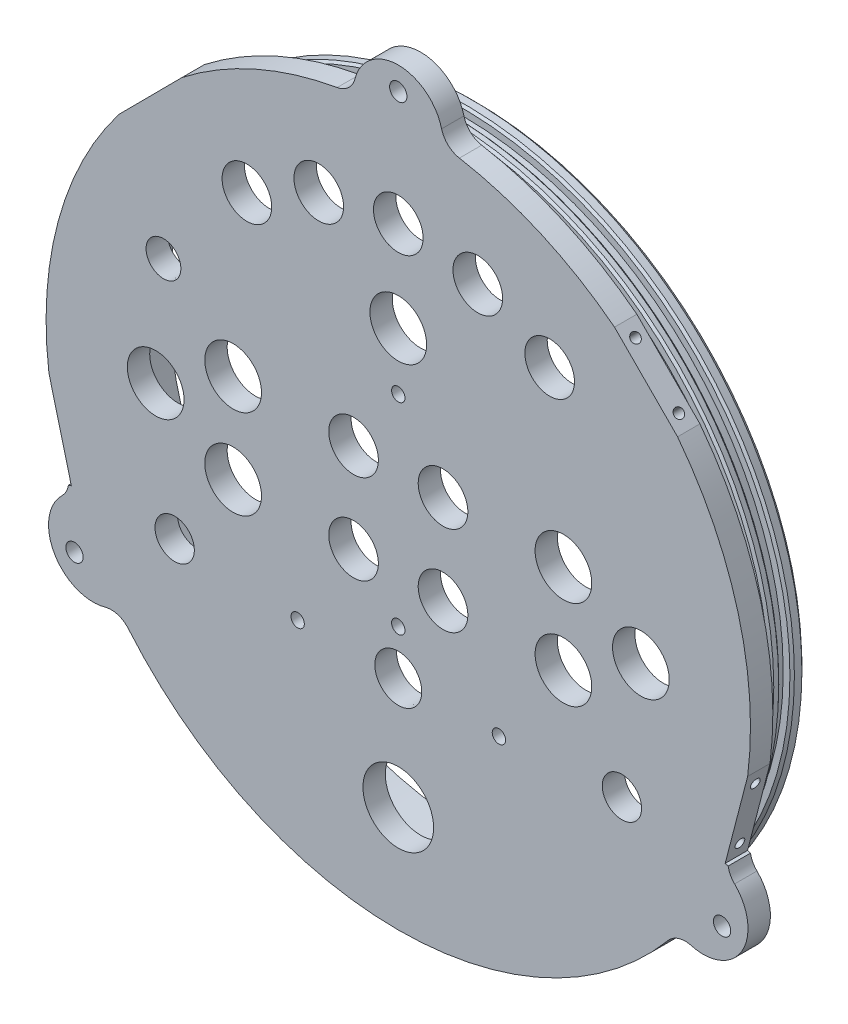
SolidWorks part; units mm, degrees
material "6061 Alloy"
ref_plane "Front Plane" through (0, 0, 0) normal (0, 0, 1) x (1, 0, 0)
ref_plane "Top Plane" through (0, 0, 0) normal (0, 1, 0) x (1, 0, 0)
ref_plane "Right Plane" through (0, 0, 0) normal (1, 0, 0) x (0, 0, -1)
sketch "Sketch1" plane through (0, 0, 0) normal (0, 0, 1) x (1, 0, 0)
  circle A0 centre (0, 0) radius 100.0125
extrude "Extrude1" add sketch "Sketch1" along normal blind 6.35
sketch "Sketch2" plane through (0, 0, 0) normal (0, 0, -1) x (-1, 0, 0)
  circle A0 centre (0, 0) radius 93.6625
extrude "Extrude2" add sketch "Sketch2" along normal blind 15.875
sketch "Sketch3" plane through (0, 0, -15.875) normal (0, 0, -1) x (-1, 0, 0)
  circle A0 centre (0, 0) radius 87.3125
extrude "Cut-Extrude1" cut sketch "Sketch3" against normal blind 15.875
sketch "Sketch4" plane through (0, 0, 0) normal (1, 0, 0) x (0, 0, -1)
  line L0 (15.875, 93.6625) -> (0, 93.6625) construction
  line L1 (2.8084, 93.6625) -> (5.9834, 93.6625)
  line L2 (2.8084, 93.6625) -> (2.8084, 91.1225)
  line L3 (2.8084, 91.1225) -> (5.9834, 91.1225)
  line L4 (5.9834, 93.6625) -> (5.9834, 91.1225)
  line L5 (0, 0) -> (42.3826, 0) construction
  line L6 (8.6645, 93.6625) -> (11.8395, 93.6625)
  line L7 (8.6645, 93.6625) -> (8.6645, 91.1225)
  line L8 (8.6645, 91.1225) -> (11.8395, 91.1225)
  line L9 (11.8395, 93.6625) -> (11.8395, 91.1225)
  dimension "D1" = 2.54
  dimension "D2" = 3.175
revolve "Cut-Revolve1" cut sketch "Sketch4" angle 360 about L5
chamfer "Chamfer1" distance 1.27 angle 45 1 edges at (-93.6625, 0, -15.875)
sketch "Sketch5" plane through (0, 0, 6.35) normal (0, 0, 1) x (1, 0, 0)
  circle A16 centre (0, 47.9573) radius 8.05
  circle A17 centre (0, 73.66) radius 7.05
  circle A18 centre (-63.5, -35.56) radius 5.588
  circle A19 centre (63.5, -35.56) radius 5.588
  dimension "D1" = 63.5
  dimension "D5" = 35.56
  dimension "D2" = 63.5
  dimension "D4" = 73.66
  dimension "D6" = 35.56
sketch "Sketch7" plane through (0, 0, 6.35) normal (0, 0, 1) x (1, 0, 0)
  line L0 (0, 0) -> (0, 100.0125) construction
  circle A0 centre (0, 0) radius 100.0125 construction
sketch "Sketch8" plane through (0, 0, 6.35) normal (0, 0, 1) x (1, 0, 0)
  line L0 (0, 0) -> (86.6134, -50.0063) construction
  line L1 (0, 0) -> (-86.6134, -50.0063) construction
  line L2 (0, 0) -> (0, 100.0125) construction
  circle A0 centre (0, 0) radius 100.0125 construction
  arc A1 (-12.6744, 99.2062) -> (12.6744, 99.2062) centre (0, 100.0125) cw
  arc A2 (92.2522, -38.6267) -> (79.5779, -60.5794) centre (86.6134, -50.0063) cw
  arc A3 (-92.2522, -38.6267) -> (-79.5779, -60.5794) centre (-86.6134, -50.0063) ccw
  arc A4 (-12.6744, 99.2062) -> (12.6744, 99.2062) centre (0, 0) cw
  arc A5 (92.2522, -38.6267) -> (79.5779, -60.5794) centre (0, 0) cw
  arc A6 (-92.2522, -38.6267) -> (-79.5779, -60.5794) centre (0, 0) ccw
  dimension "D1" = 12.7
  dimension "D2" = 12.7
  dimension "D3" = 12.7
  dimension "D4" = 120
  dimension "D5" = 120
extrude "Extrude3" add sketch "Sketch8" against normal up to surface (6.35 mm away) up to face at (100.0125, 0, 0)
sketch "Sketch10" plane through (0, 0, 6.35) normal (0, 0, 1) x (1, 0, 0)
  line L0 (0, 0) -> (0, 123.4907) construction
  line L1 (0, 0) -> (137.3268, -79.2857) construction
  line L2 (0, 0) -> (-146.5837, -84.6301) construction
extrude "Cut-Extrude2" cut sketch "Sketch5" against normal through all
hole_wizard "#10 (0.1935) Diameter Hole1" positions "3DSketch2" profile "Sketch11" hole size "#10" standard "Ansi Inch"
sketch3d "3DSketch2"
  line L0 (0, 0, 6.35) -> (0, 123.4907, 6.35) construction
  line L1 (0, 0, 6.35) -> (137.3268, -79.2857, 6.35) construction
  line L2 (0, 0, 6.35) -> (-146.5837, -84.6301, 6.35) construction
  point P0 (0, 106.1728, 6.35)
  point P4 (91.9483, -53.0864, 6.35)
  point P8 (-91.9483, -53.0864, 6.35)
  dimension "D1" = 106.3625
  dimension "D2" = 106.3625
  dimension "D3" = 106.3625
sketch "Sketch11" plane through (0, 106.1728, 6.35) normal (1, 0, 0) x (0, -1, 0)
  line L0 (0, 0) -> (0, 331.6766)
  line L1 (0, 331.6766) -> (2.4574, 330.2)
  line L2 (2.4574, 330.2) -> (2.4574, 0)
  line L5 (2.4574, 0) -> (0, 0)
  line L10 (0, 331.6766) -> (-2.4575, 330.2) construction
  line L11 (0, -6.35) -> (0, 107.95) construction
  dimension "Hole Dia." = 4.9149
  dimension "Hole Depth" = 330.2
  dimension "Drill Angle" = 118
chamfer "Chamfer2" distance 0.635 angle 45 4 edges at (93.6625, 0, -2.8084) (93.6625, 0, -5.9834) (93.6625, 0, -8.6645) (93.6625, 0, -11.8395)
sketch "Sketch15" plane through (0, 0, 6.35) normal (0, 0, 1) x (1, 0, 0)
  circle A0 centre (0, -69.85) radius 10.033
  dimension "D1" = 69.85
extrude "Cut-Extrude3" cut sketch "Sketch15" against normal through all
sketch "Sketch17" plane through (0, 0, 6.35) normal (0, 0, 1) x (1, 0, 0)
  line L0 (0, 106.1728) -> (0, 0) construction
  line L1 (-46.896, 12.7) -> (-46.896, -12.7) construction
  line L2 (-46.896, 0) -> (-107.9684, 0) construction
  line L3 (46.896, 0) -> (107.9684, 0) construction
  line L4 (46.896, 12.7) -> (46.896, -12.7) construction
  line L5 (0, 0) -> (-129.2921, 0) construction
  line L6 (68.8931, 0) -> (46.896, 12.7) construction
  line L7 (42.9911, 59.8127) -> (22.5831, 70.1128) construction
  line L8 (22.5831, 70.1128) -> (0, 73.66) construction
  line L9 (22.5831, 70.1128) -> (30.6624, 95.1962) construction
  line L10 (30.6624, 95.1962) -> (60.9252, 85.4486) construction
  line L11 (42.9911, 59.8127) -> (58.3716, 81.2112) construction
  line L12 (58.3716, 81.2112) -> (94.3714, 55.3359) construction
  line L13 (0, 0) -> (22.5831, 70.1128) construction
  line L14 (22.5831, 70.1128) -> (0, 73.66) construction
  line L15 (0, 73.66) -> (0, 0) construction
  line L16 (12.7, -12.7) -> (12.7, 0) construction
  line L17 (12.7, 12.7) -> (0, 12.7) construction
  line L19 (12.7, 0) -> (12.7, 12.7) construction
  circle A0 centre (-22.5831, 70.1128) radius 7.05
  circle A1 centre (-42.9911, 59.8127) radius 7.05
  circle A2 centre (-68.8931, 0) radius 8.05
  circle A3 centre (-46.896, -12.7) radius 8.05
  circle A4 centre (-46.896, 12.7) radius 8.05
  circle A5 centre (-12.7, 12.7) radius 7.05
  circle A6 centre (-12.7, -12.7) radius 7.05
  circle A7 centre (12.7, -12.7) radius 7.05
  circle A8 centre (12.7, 12.7) radius 7.05
  circle A9 centre (46.896, 12.7) radius 8.05
  circle A10 centre (46.896, -12.7) radius 8.05
  circle A11 centre (68.8931, 0) radius 8.05
  circle A12 centre (42.9911, 59.8127) radius 7.05
  circle A13 centre (22.5831, 70.1128) radius 7.05
  circle A15 centre (0, 0) radius 100.0125 construction
  dimension "D1" = 25.4
  dimension "D2" = 25.4
  dimension "D3" = 25.4
  dimension "D4" = 22.86
extrude "Cut-Extrude4" cut sketch "Sketch17" against normal through all
hole_wizard "#6 Clearance Hole1" positions "3DSketch7" profile "Sketch18" hole size "#6" standard "Ansi Inch"
sketch3d "3DSketch7"
  line L0 (0, 0, 0) -> (55.3338, 0, 0) construction
  line L2 (0, 0, 0) -> (0, -54.9677, 0) construction
  point P17 (28.575, -38.1, 0)
  point P19 (-28.575, -38.1, 0)
  dimension "D1" = 57.15
  dimension "D3" = 38.1
  dimension "D2" = 28.575
sketch "Sketch18" plane through (28.575, -38.1, 0) normal (1, 0, 0) x (0, 1, 0)
  line L0 (0, 0) -> (0, 13.8408)
  line L1 (0, 13.8408) -> (1.8986, 12.7)
  line L2 (1.8986, 12.7) -> (1.8986, 0)
  line L5 (1.8986, 0) -> (0, 0)
  line L10 (0, 13.8408) -> (-1.8987, 12.7) construction
  line L11 (0, -6.35) -> (0, 107.95) construction
  dimension "Hole Dia." = 3.7973
  dimension "Hole Depth" = 12.7
  dimension "Drill Angle" = 118
hole_wizard "Tap Drill for #6 Tap1" positions "3DSketch8" profile "Sketch19" hole size "#6-32" standard "Ansi Inch"
sketch3d "3DSketch8"
  line L0 (0, 0, 0) -> (-45.7945, 0, 0) construction
  line L2 (0, 0, 0) -> (0, 34.2452, 0) construction
  point P0 (34.925, 29.21, 0)
  point P2 (-34.925, 29.21, 0)
  point P4 (-25.4, 29.21, 0)
  point P6 (25.4, 29.21, 0)
  point P15 (44.45, -52.705, 0)
  point P17 (-44.45, -52.705, 0)
  dimension "D1" = 9.525
  dimension "D2" = 9.525
  dimension "D3" = 69.85
  dimension "D4" = 34.925
  dimension "D5" = 29.21
  dimension "D6" = 88.9
  dimension "D7" = 52.705
  dimension "D8" = 44.45
sketch "Sketch19" plane through (34.925, 29.21, 0) normal (1, 0, 0) x (0, 1, 0)
  line L0 (0, 0) -> (0, 4.1147)
  line L1 (0, 4.1147) -> (1.3525, 3.302)
  line L2 (1.3525, 3.302) -> (1.3525, 0)
  line L5 (1.3525, 0) -> (0, 0)
  line L10 (0, 4.1147) -> (-1.3526, 3.302) construction
  line L11 (0, -6.35) -> (0, 107.95) construction
  dimension "Hole Dia." = 2.7051
  dimension "Hole Depth" = 3.302
  dimension "Drill Angle" = 118
hole_wizard "1/4 NPT Tapped Hole1" positions "3DSketch9" profile "Sketch20" size "1/4" standard "Ansi Inch"
sketch3d "3DSketch9"
  line L0 (0, 0, 0) -> (0, -87.3125, 0) construction
  line L2 (0, 0, 0) -> (87.3125, 0, 0) construction
  circle A0 centre (0, 0, 0) radius 87.3125 construction
  point P9 (0, -38.1, 0)
  point P20 (0, 0, -87.3125)
  dimension "D2" = 38.1
sketch "Sketch20" plane through (0, -38.1, 0) normal (1, 0, 0) x (0, 1, 0)
  line L0 (0, 0) -> (0, 20.3603)
  line L1 (5.5626, 17.018) -> (0, 20.3603)
  line L2 (-5.5626, 17.018) -> (0, 20.3603) construction
  line L3 (5.5626, 17.018) -> (5.5626, 9.906)
  line L4 (5.5626, 9.906) -> (6.558, 9.906)
  line L5 (6.558, 9.906) -> (6.8546, 0)
  line L6 (-6.558, 9.906) -> (-6.8546, 0) construction
  line L7 (6.8546, 0) -> (0, 0)
  line L8 (0, -6.35) -> (0, 107.95) construction
  line L11 (-5.5626, 9.906) -> (-6.558, 9.906) construction
  dimension "Tap Drill Dia." = 11.1252
  dimension "Tap Drill Depth" = 17.018
  dimension "Thread Dia." = 13.7092
  dimension "Thread Angle" = 3.43
  dimension "Thread Depth" = 9.906
  dimension "Drill Angle" = 118
hole_wizard "1/8 NPT Tapped Hole1" positions "3DSketch6" profile "Sketch16" size "1/8" standard "Ansi Inch"
sketch3d "3DSketch6"
  line L0 (0, 0, 0) -> (87.3125, 0, 0) construction
  line L2 (0, 0, 0) -> (0, 87.3125, 0) construction
  circle A0 centre (0, 0, 0) radius 87.3125 construction
  point P3 (-66.675, 31.75, 0)
  point P10 (0, 0, -87.3125)
  dimension "D1" = 31.75
  dimension "D2" = 66.675
sketch "Sketch16" plane through (-66.675, 31.75, 0) normal (1, 0, 0) x (0, 1, 0)
  line L0 (0, 0) -> (0, 13.7095)
  line L1 (4.2164, 11.176) -> (0, 13.7095)
  line L2 (-4.2164, 11.176) -> (0, 13.7095) construction
  line L3 (4.2164, 11.176) -> (4.2164, 6.35)
  line L4 (4.2164, 6.35) -> (4.9362, 6.35)
  line L5 (4.9362, 6.35) -> (5.1263, 0)
  line L6 (-4.9362, 6.35) -> (-5.1263, 0) construction
  line L7 (5.1263, 0) -> (0, 0)
  line L8 (0, -6.35) -> (0, 107.95) construction
  line L11 (-4.2164, 6.35) -> (-4.9362, 6.35) construction
  dimension "Tap Drill Dia." = 8.4328
  dimension "Tap Drill Depth" = 11.176
  dimension "Thread Dia." = 10.2526
  dimension "Thread Angle" = 3.43
  dimension "Thread Depth" = 6.35
  dimension "Drill Angle" = 118
fillet "Fillet1" radius 6.35 6 edges at (92.2522, -38.6267, 3.175) (79.5779, -60.5794, 3.175) (-12.6744, 99.2062, 3.175) (12.6744, 99.2062, 3.175) (-79.5779, -60.5794, 3.175) (-92.2522, -38.6267, 3.175)
sketch "Sketch22" plane through (0, 0, 6.35) normal (0, 0, 1) x (1, 0, 0)
  line L0 (0, 0) -> (0, 100.0125) construction
  line L1 (-79.302, 60.94) -> (-70.3475, 69.946)
  line L2 (-70.9217, 70.5168) -> (0, 0) construction
  line L3 (0, 0) -> (-96.8054, -25.1239) construction
  line L4 (-70.3475, 69.946) -> (-61.393, 78.9519)
  line L5 (-99.2121, -12.6278) -> (-96.0218, -24.9205)
  line L6 (-96.0218, -24.9205) -> (-92.8314, -37.2133)
  line L7 (-79.302, 60.94) -> (-84.7318, 66.3388)
  line L8 (-66.8227, 84.3506) -> (-61.393, 78.9519)
  line L9 (-84.7318, 66.3388) -> (-66.8227, 84.3506)
  line L10 (-92.8314, -37.2133) -> (-99.2121, -38.8693)
  line L11 (-99.2121, -38.8693) -> (-105.5928, -14.2838)
  line L12 (-105.5928, -14.2838) -> (-99.2121, -12.6278)
  line L13 (105.5928, -14.2838) -> (99.2121, -12.6278)
  line L14 (99.2121, -38.8693) -> (105.5928, -14.2838)
  line L15 (92.8314, -37.2133) -> (99.2121, -38.8693)
  line L16 (84.7318, 66.3388) -> (66.8227, 84.3506)
  line L17 (66.8227, 84.3506) -> (61.393, 78.9519)
  line L18 (79.302, 60.94) -> (84.7318, 66.3388)
  line L19 (96.0218, -24.9205) -> (92.8314, -37.2133)
  line L20 (99.2121, -12.6278) -> (96.0218, -24.9205)
  line L21 (70.3475, 69.946) -> (61.393, 78.9519)
  line L22 (79.302, 60.94) -> (70.3475, 69.946)
  circle A0 centre (0, 0) radius 100.0125 construction
  dimension "D1" = 45.164
  dimension "D2" = 104.549
  dimension "D3" = 25.4
  dimension "D4" = 25.4
  dimension "D5" = 12.7
  dimension "D6" = 12.7
extrude "Cut-Extrude5" cut sketch "Sketch22" against normal through all
hole_wizard "Tap Drill for #6 Tap2" positions "3DSketch11" profile "Sketch23" hole size "#6-32" standard "Ansi Inch"
sketch3d "3DSketch11"
  line L0 (61.393, 78.9519, 3.175) -> (79.302, 60.94, 3.175) construction
  line L1 (61.393, 78.9519, 0) -> (61.393, 78.9519, 6.35) construction
  line L2 (79.302, 60.94, 0) -> (79.302, 60.94, 6.35) construction
  line L4 (99.2121, -12.6278, 3.175) -> (92.8314, -37.2133, 3.175) construction
  line L5 (99.2121, -12.6278, 0) -> (99.2121, -12.6278, 6.35) construction
  line L6 (92.8314, -37.2133, 0) -> (92.8314, -37.2133, 6.35) construction
  line L8 (-92.8314, -37.2133, 3.175) -> (-99.2121, -12.6278, 3.175) construction
  line L9 (-92.8314, -37.2133, 0) -> (-92.8314, -37.2133, 6.35) construction
  line L10 (-99.2121, -12.6278, 0) -> (-99.2121, -12.6278, 6.35) construction
  line L12 (-61.393, 78.9519, 3.175) -> (-79.302, 60.94, 3.175) construction
  line L13 (-61.393, 78.9519, 0) -> (-61.393, 78.9519, 6.35) construction
  line L14 (-79.302, 60.94, 0) -> (-79.302, 60.94, 6.35) construction
  line L16 (-96.0218, -24.9205, 6.35) -> (-96.0218, -24.9205, 0) construction
  line L17 (-92.8314, -37.2133, 6.35) -> (-99.2121, -12.6278, 6.35) construction
  line L18 (-92.8314, -37.2133, 0) -> (-99.2121, -12.6278, 0) construction
  line L20 (-70.3475, 69.946, 6.35) -> (-70.3475, 69.946, 0) construction
  line L21 (-79.302, 60.94, 6.35) -> (-61.393, 78.9519, 6.35) construction
  line L22 (-79.302, 60.94, 0) -> (-61.393, 78.9519, 0) construction
  line L24 (70.3475, 69.946, 6.35) -> (70.3475, 69.946, 0) construction
  line L25 (61.393, 78.9519, 6.35) -> (79.302, 60.94, 6.35) construction
  line L26 (61.393, 78.9519, 0) -> (79.302, 60.94, 0) construction
  line L28 (96.0218, -24.9205, 6.35) -> (96.0218, -24.9205, 0) construction
  line L29 (99.2121, -12.6278, 6.35) -> (92.8314, -37.2133, 6.35) construction
  line L30 (99.2121, -12.6278, 0) -> (92.8314, -37.2133, 0) construction
  point P0 (-93.8284, -33.3718, 3.175)
  point P2 (-98.2151, -16.4693, 3.175)
  point P4 (-76.5038, 63.7544, 3.175)
  point P6 (-64.1913, 76.1375, 3.175)
  point P8 (64.1913, 76.1375, 3.175)
  point P10 (76.5038, 63.7544, 3.175)
  point P12 (98.2151, -16.4693, 3.175)
  point P14 (93.8284, -33.3718, 3.175)
  dimension "D1" = 17.4625
  dimension "D2" = 8.7312
  dimension "D3" = 17.4625
  dimension "D4" = 8.7312
  dimension "D5" = 17.4625
  dimension "D6" = 8.7312
  dimension "D7" = 17.4625
  dimension "D8" = 8.7312
sketch "Sketch23" plane through (-93.8284, -33.3718, 3.175) normal (0, 0, 1) x (0.2512, -0.9679, 0)
  line L0 (0, 0) -> (0, 10.3377)
  line L1 (0, 10.3377) -> (1.3525, 9.525)
  line L2 (1.3525, 9.525) -> (1.3525, 0)
  line L5 (1.3525, 0) -> (0, 0)
  line L10 (0, 10.3377) -> (-1.3526, 9.525) construction
  line L11 (0, -6.35) -> (0, 107.95) construction
  dimension "Hole Dia." = 2.7051
  dimension "Hole Depth" = 9.525
  dimension "Drill Angle" = 118
hole_wizard "#6 Clearance Hole2" positions "Sketch25" profile "Sketch24" hole size "#6" standard "Ansi Inch"
sketch "Sketch25" plane through (0, 0, 6.35) normal (0, 0, 1) x (1, 0, 0)
  line L0 (0, 112.7125) -> (0, -100.0125) construction
  arc A0 (12.301, 103.1707) -> (-12.301, 103.1707) centre (0, 100.0125) ccw construction
  arc A1 (-76.6251, -64.2736) -> (76.6251, -64.2736) centre (0, 0) ccw construction
  point P0 (0, 31.75)
  point P1 (0, -25.4)
  dimension "D1" = 57.15
  dimension "D2" = 31.75
sketch "Sketch24" plane through (0, 31.75, 6.35) normal (1, 0, 0) x (0, -1, 0)
  line L0 (0, 0) -> (0, 7.4908)
  line L1 (0, 7.4908) -> (1.8986, 6.35)
  line L2 (1.8986, 6.35) -> (1.8986, 0)
  line L5 (1.8986, 0) -> (0, 0)
  line L10 (0, 7.4908) -> (-1.8986, 6.35) construction
  line L11 (0, -6.35) -> (0, 107.95) construction
  dimension "Hole Dia." = 3.7973
  dimension "Hole Depth" = 6.35
  dimension "Drill Angle" = 118
